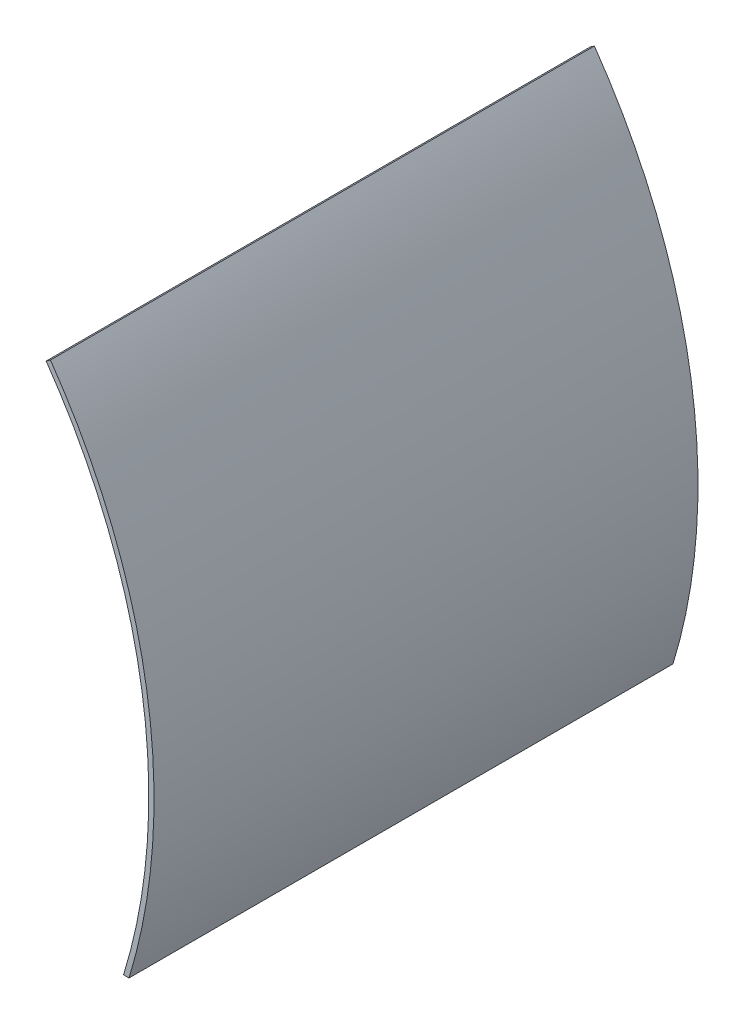
SolidWorks part; units mm, degrees
material "PE High Density"
ref_plane "Front Plane" through (0, 0, 0) normal (0, 0, 1) x (1, 0, 0)
ref_plane "Top Plane" through (0, 0, 0) normal (0, 1, 0) x (1, 0, 0)
ref_plane "Right Plane" through (0, 0, 0) normal (1, 0, 0) x (0, 0, -1)
sketch "Sketch1" plane through (0, 0, 0) normal (0, 0, 1) x (1, 0, 0)
  line L0 (0, 0) -> (172.2438, 0) construction
  line L1 (0, 0) -> (141.0938, 98.795) construction
  line L2 (172.2438, 0) -> (173.8312, 0) construction
  line L3 (141.0938, 98.795) -> (142.3942, 99.7055)
  line L4 (172.2438, 0) -> (172.2438, -50.8) construction
  line L5 (164.5821, -50.8) -> (172.2438, -50.8) construction
  line L6 (166.2428, -50.8) -> (164.5821, -50.8)
  arc A0 (172.2438, 0) -> (141.0938, 98.795) centre (0, 0) ccw
  arc A1 (173.8312, 0) -> (142.3942, 99.7055) centre (0, 0) ccw
  arc A2 (172.2438, 0) -> (164.5821, -50.8) centre (0, 0) cw
  arc A3 (173.8312, 0) -> (166.2428, -50.8) centre (0, 0) cw
  dimension "D2" = 35
  dimension "D3" = 1.5875
  dimension "D1" = 172.2438
  dimension "D4" = 50.8
extrude "Boss-Extrude1" add sketch "Sketch1" along normal blind 165.1
